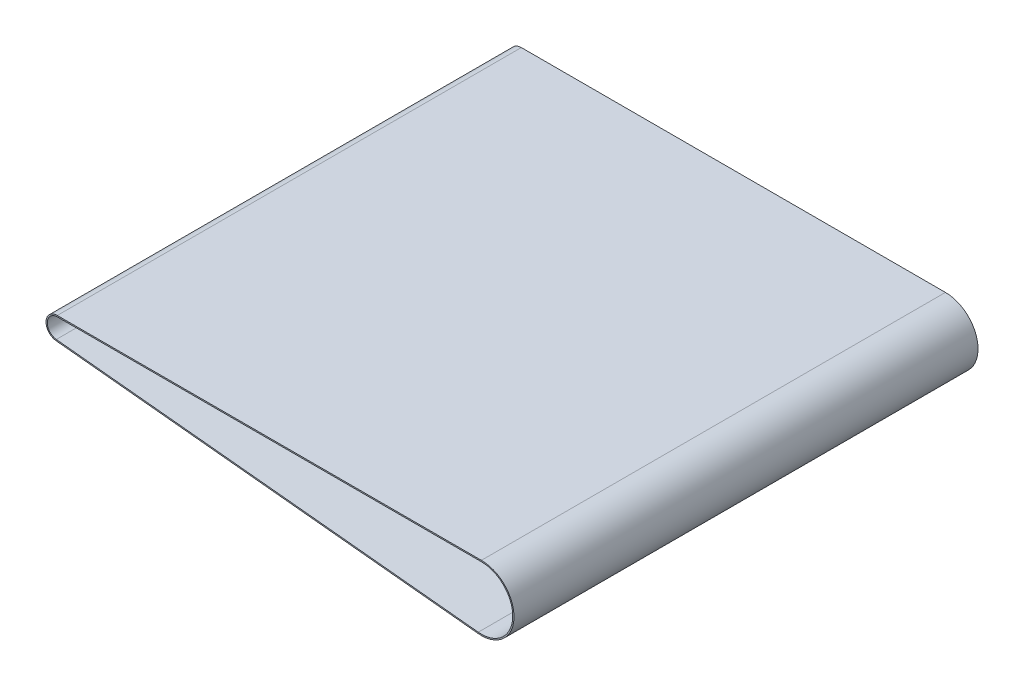
SolidWorks part; units mm, degrees
ref_plane "前视基准面" through (0, 0, 0) normal (0, 0, 1) x (1, 0, 0)
ref_plane "上视基准面" through (0, 0, 0) normal (0, 1, 0) x (1, 0, 0)
ref_plane "右视基准面" through (0, 0, 0) normal (1, 0, 0) x (0, 0, -1)
sketch "草图1" plane through (0, 0, 0) normal (0, 0, 1) x (1, 0, 0)
  line L0 (-54.5025, 0) -> (77.9283, 0) construction
  line L1 (-24.2462, 0) -> (313.9268, 0)
  line L2 (-25.0484, -15.9597) -> (311.4196, -49.874)
  line L3 (-24.2462, 1) -> (313.9268, 1)
  line L4 (-25.1487, -16.9546) -> (311.3194, -50.8689)
  arc A0 (-24.2462, 0) -> (-25.0484, -15.9597) centre (-24.2462, -8) ccw
  arc A1 (311.4196, -49.874) -> (313.9268, 0) centre (313.9268, -25) ccw
  arc A2 (-24.2462, 1) -> (-25.1487, -16.9546) centre (-24.2462, -8) ccw
  arc A3 (311.3194, -50.8689) -> (313.9268, 1) centre (313.9268, -25) ccw
  dimension "D1" = 16
  dimension "D2" = 50
  dimension "D4" = 18
  dimension "D5" = 52
  dimension "D3" = 338.6
extrude "凸台-拉伸1" add sketch "草图1" along normal blind 370
